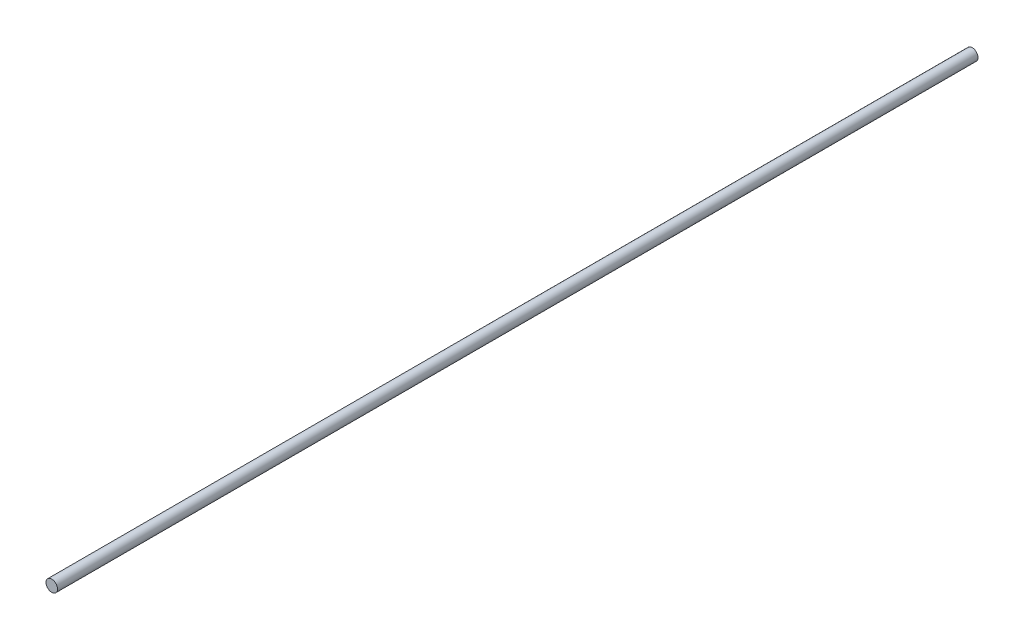
SolidWorks part; units mm, degrees
ref_plane "Plan de face" through (0, 0, 0) normal (0, 0, 1) x (1, 0, 0)
ref_plane "Plan de dessus" through (0, 0, 0) normal (0, 1, 0) x (1, 0, 0)
ref_plane "Plan de droite" through (0, 0, 0) normal (1, 0, 0) x (0, 0, -1)
sketch "Esquisse1" plane through (0, 0, 0) normal (0, 0, 1) x (1, 0, 0)
  circle A0 centre (0, 0) radius 4
  dimension "D1" = 8
extrude "Boss.-Extru.1" add sketch "Esquisse1" along normal blind 640
